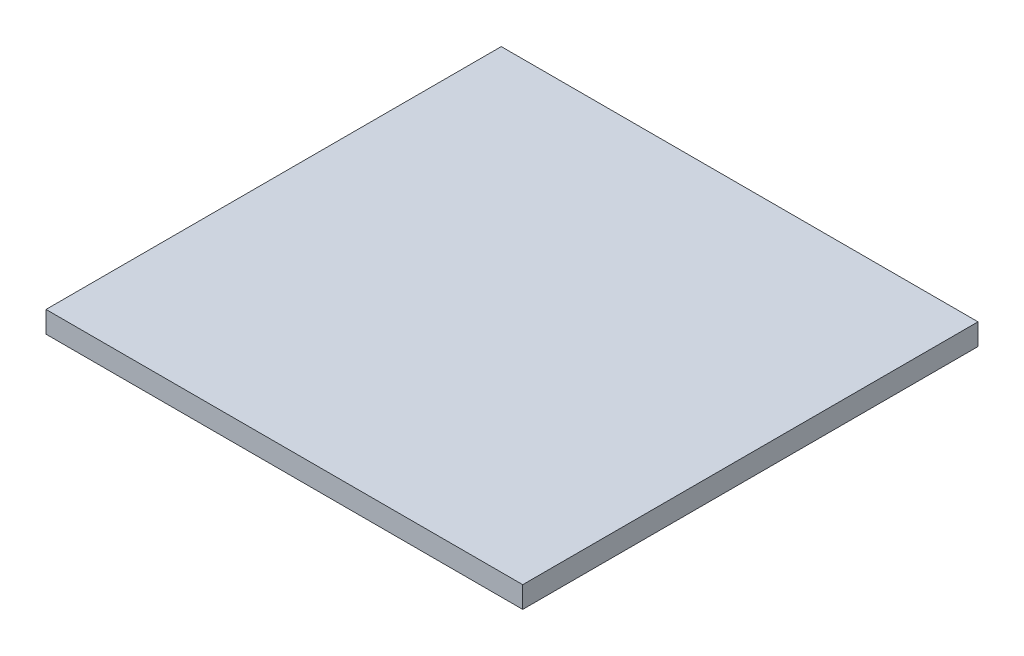
SolidWorks part; units mm, degrees
ref_plane "前视基准面" through (0, 0, 0) normal (0, 0, 1) x (1, 0, 0)
ref_plane "上视基准面" through (0, 0, 0) normal (0, 1, 0) x (1, 0, 0)
ref_plane "右视基准面" through (0, 0, 0) normal (1, 0, 0) x (0, 0, -1)
other "Configuration Table"
sketch "草图1" plane through (0, 0, 0) normal (0, 1, 0) x (1, 0, 0)
  line L1 (-100, 95.5) -> (100, 95.5)
  line L2 (-100, 95.5) -> (-100, -95.5)
  line L3 (-100, -95.5) -> (100, -95.5)
  line L4 (100, 95.5) -> (100, -95.5)
  line L5 (-100, 95.5) -> (100, -95.5) construction
  line L6 (-100, -95.5) -> (100, 95.5) construction
  point P0 (0, 0)
  dimension "D1" = 200
  dimension "D2" = 191
extrude "凸台-拉伸1" add sketch "草图1" along normal blind 9
